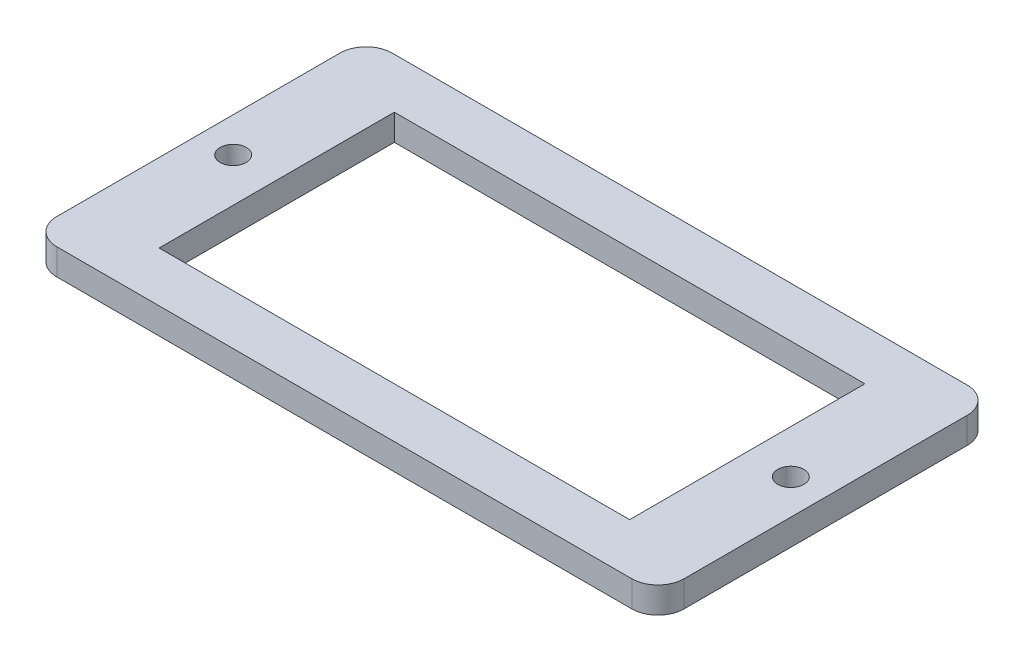
SolidWorks part; units mm, degrees
material "Lasercut ABS"
ref_plane "Front Plane" through (0, 0, 0) normal (0, 0, 1) x (1, 0, 0)
ref_plane "Top Plane" through (0, 0, 0) normal (0, 1, 0) x (1, 0, 0)
ref_plane "Right Plane" through (0, 0, 0) normal (1, 0, 0) x (0, 0, -1)
sketch "Sketch1" plane through (0, 0, 0) normal (0, 1, 0) x (1, 0, 0)
  line L0 (-32, 0) -> (32, 0) construction
  line L1 (-36, 19.25) -> (36, 19.25)
  line L2 (-36, 19.25) -> (-36, -19.25)
  line L3 (-36, -19.25) -> (36, -19.25)
  line L4 (36, 19.25) -> (36, -19.25)
  line L5 (-27, 13.5) -> (27, 13.5)
  line L6 (-27, 13.5) -> (-27, -13.5)
  line L7 (-27, -13.5) -> (27, -13.5)
  line L8 (27, 13.5) -> (27, -13.5)
  circle A0 centre (-32, 0) radius 1.5
  circle A1 centre (32, 0) radius 1.5
  point P8 (0, 19.25)
  point P10 (36, 0)
  point P11 (0, 13.5)
  point P12 (27, 0)
  point P17 (0, 0)
  dimension "D6" = 3
  dimension "D1" = 72
  dimension "D2" = 38.5
  dimension "D3" = 27
  dimension "D4" = 54
  dimension "D5" = 64
extrude "Boss-Extrude1" add sketch "Sketch1" along normal blind 3
fillet "Fillet1" radius 3 4 edges at (-36, 1.5, -19.25) (36, 1.5, -19.25) (36, 1.5, 19.25) (-36, 1.5, 19.25)
